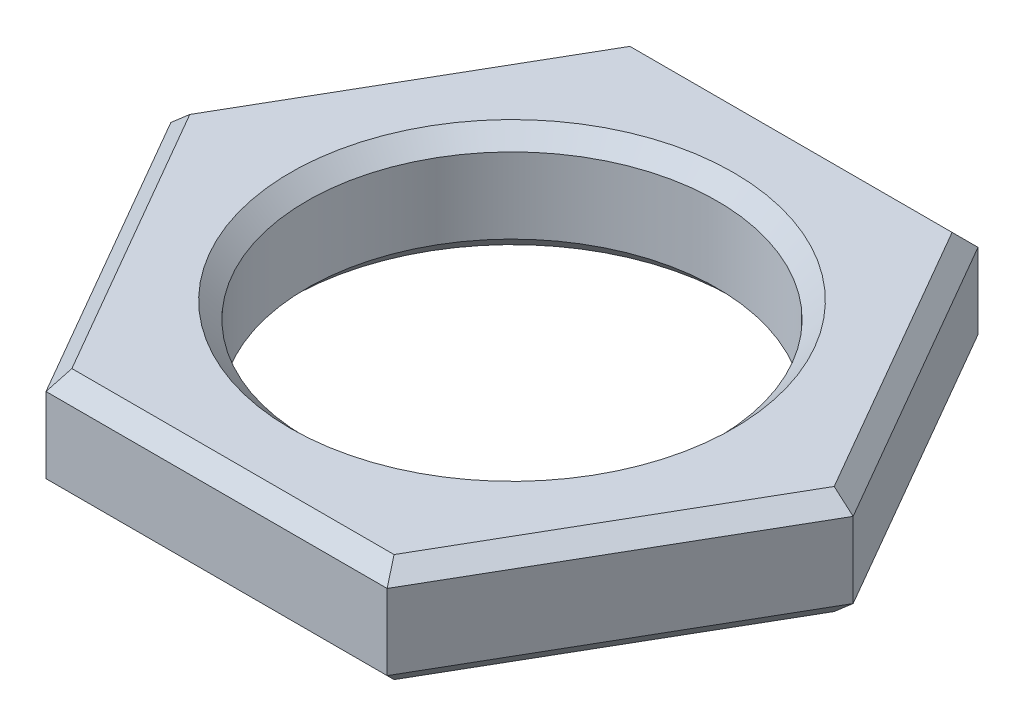
SolidWorks part; units mm, degrees
ref_plane "Front Plane" through (0, 0, 0) normal (0, 0, 1) x (1, 0, 0)
ref_plane "Top Plane" through (0, 0, 0) normal (0, 1, 0) x (1, 0, 0)
ref_plane "Right Plane" through (0, 0, 0) normal (1, 0, 0) x (0, 0, -1)
sketch "Sketch1" plane through (0, 0, 0) normal (0, 1, 0) x (1, 0, 0)
  line L1 (5.1962, 0) -> (2.5981, 4.5)
  line L2 (2.5981, 4.5) -> (-2.5981, 4.5)
  line L3 (-2.5981, 4.5) -> (-5.1962, 0)
  line L4 (-5.1962, 0) -> (-2.5981, -4.5)
  line L5 (-2.5981, -4.5) -> (2.5981, -4.5)
  line L6 (2.5981, -4.5) -> (5.1962, 0)
  circle A0 centre (0, 0) radius 4.5 construction
  circle A1 centre (0, 0) radius 3.125
  dimension "D2" = 6.25
  dimension "D1" = 9
extrude "Boss-Extrude1" add sketch "Sketch1" along normal blind 1.65
chamfer "Chamfer1" distance 0.25 angle 45 14 edges at (0, 0, 3.125) (3.8971, 0, -2.25) (0, 0, -4.5) (-3.8971, 0, -2.25) (-3.8971, 0, 2.25) (0, 0, 4.5) (3.8971, 0, 2.25) (0, 1.65, 3.125) (0, 1.65, 4.5) (-3.8971, 1.65, 2.25) (-3.8971, 1.65, -2.25) (0, 1.65, -4.5) (3.8971, 1.65, -2.25) (3.8971, 1.65, 2.25)
